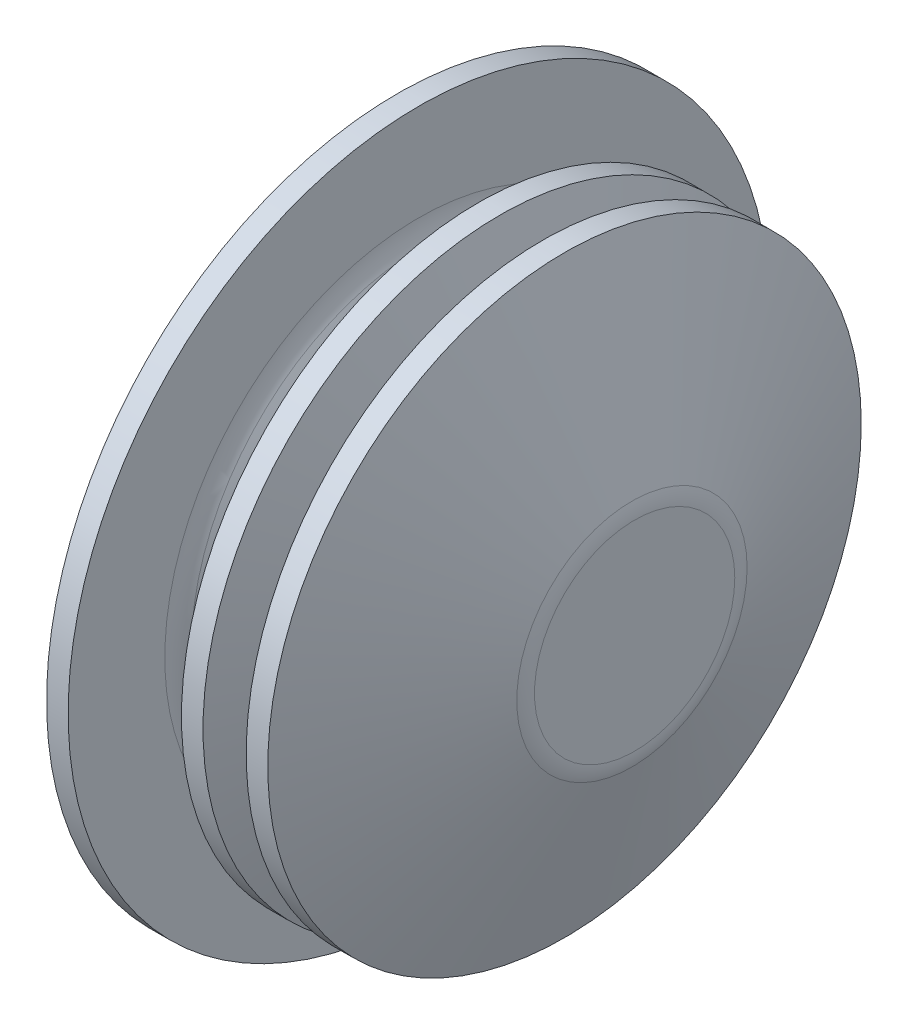
SolidWorks part; units mm, degrees
ref_plane "Front Plane" through (0, 0, 0) normal (0, 0, 1) x (1, 0, 0)
ref_plane "Top Plane" through (0, 0, 0) normal (0, 1, 0) x (1, 0, 0)
ref_plane "Right Plane" through (0, 0, 0) normal (1, 0, 0) x (0, 0, -1)
sketch "Sketch2" plane through (0, 0, 0) normal (0, 1, 0) x (1, 0, 0)
  line L0 (0, 0) -> (0, 13)
  line L1 (0, 13) -> (0.8, 13)
  line L2 (0.8, 13) -> (0.8, 9.4175)
  line L3 (4.5378, 4) -> (5.1685, 4)
  line L4 (5.4498, 4.4045) -> (3, 11)
  line L5 (3, 11) -> (3.8, 11)
  line L6 (3.8, 11) -> (6.0126, 5.0429)
  line L7 (7.5125, 4) -> (7.5685, 4)
  line L8 (7.8498, 4.4045) -> (5.4, 11)
  line L9 (5.4, 11) -> (6.2, 11)
  line L10 (6.2, 11) -> (8.6999, 4.2696)
  line L11 (8.8, 3.7125) -> (8.8, 0)
  line L12 (8.8, 0) -> (0, 0)
  line L13 (1.004, 8.6357) -> (3.1418, 4.8182)
  arc A0 (8.6999, 4.2696) -> (8.8, 3.7125) centre (7.2, 3.7125) cw
  arc A1 (6.0126, 5.0429) -> (7.5125, 4) centre (7.5125, 5.6) ccw
  arc A2 (3.1418, 4.8182) -> (4.5378, 4) centre (4.5378, 5.6) ccw
  arc A3 (1.004, 8.6357) -> (0.8, 9.4175) centre (2.4, 9.4175) cw
  arc A4 (7.5685, 4) -> (7.8498, 4.4045) centre (7.5685, 4.3) ccw
  arc A5 (5.1685, 4) -> (5.4498, 4.4045) centre (5.1685, 4.3) ccw
  point P19 (6.4, 4)
  point P22 (3.6, 4)
  point P25 (0.8, 9)
  point P28 (8, 4)
  point P31 (5.6, 4)
  dimension "D15" = 1.6
  dimension "D16" = 0.3
  dimension "D1" = 13
  dimension "D2" = 11
  dimension "D3" = 4.8
  dimension "D4" = 0.8
  dimension "D5" = 1.6
  dimension "D6" = 0.8
  dimension "D7" = 0.8
  dimension "D8" = 0.8
  dimension "D9" = 0.8
  dimension "D10" = 4
  dimension "D11" = 2.2
  dimension "D12" = 1.6
  dimension "D13" = 4
  dimension "D14" = 2
revolve "Revolve1" add sketch "Sketch2" angle 360 about L12
